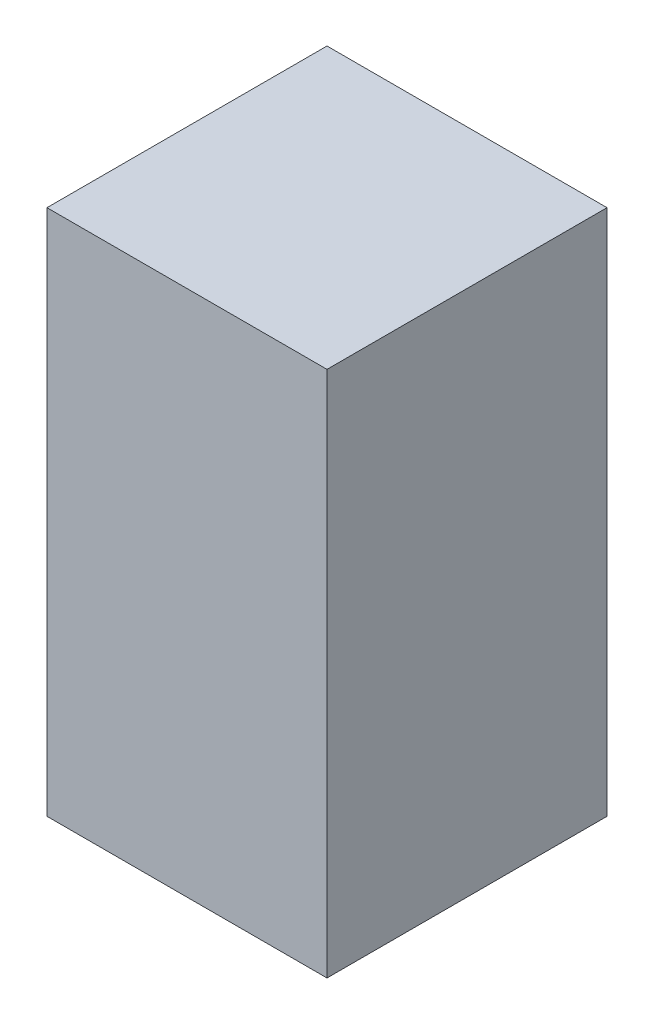
SolidWorks part; units mm, degrees
ref_plane "Front Plane" through (0, 0, 0) normal (0, 0, 1) x (1, 0, 0)
ref_plane "Top Plane" through (0, 0, 0) normal (0, 1, 0) x (1, 0, 0)
ref_plane "Right Plane" through (0, 0, 0) normal (1, 0, 0) x (0, 0, -1)
sketch "Sketch1" plane through (0, 0, 0) normal (0, 1, 0) x (1, 0, 0)
  line L1 (-26.9875, -26.9875) -> (26.9875, -26.9875)
  line L2 (-26.9875, -26.9875) -> (-26.9875, 26.9875)
  line L3 (-26.9875, 26.9875) -> (26.9875, 26.9875)
  line L4 (26.9875, -26.9875) -> (26.9875, 26.9875)
  line L5 (-26.9875, -26.9875) -> (26.9875, 26.9875) construction
  line L6 (-26.9875, 26.9875) -> (26.9875, -26.9875) construction
  point P0 (0, 0)
  dimension "D1" = 53.975
extrude "Boss-Extrude1" add sketch "Sketch1" along normal blind 101.6
